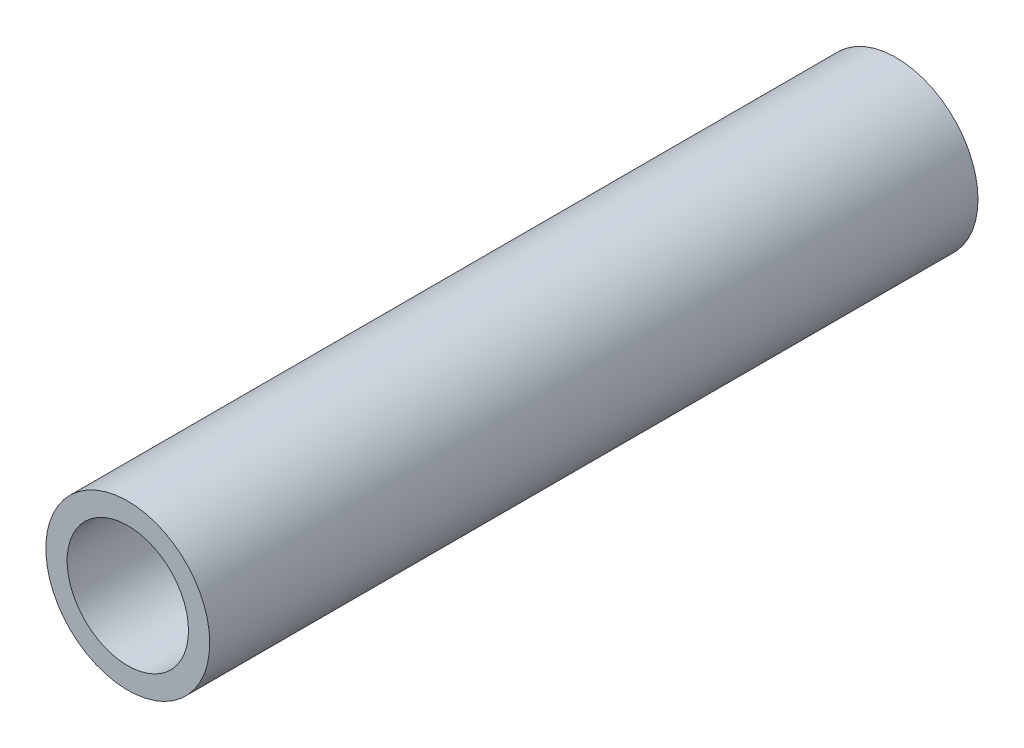
SolidWorks part; units mm, degrees
ref_plane "Front Plane" through (0, 0, 0) normal (0, 0, 1) x (1, 0, 0)
ref_plane "Top Plane" through (0, 0, 0) normal (0, 1, 0) x (1, 0, 0)
ref_plane "Right Plane" through (0, 0, 0) normal (1, 0, 0) x (0, 0, -1)
sketch "Sketch1" plane through (0, 0, 0) normal (0, 0, 1) x (1, 0, 0)
  circle A0 centre (0, 0) radius 10.668
  dimension "Pipe OD" = 21.336
extrude "Extrude-Thin1" add sketch "Sketch1" along normal mid plane 100 thin thin type one direction reverse wall 2.7686
